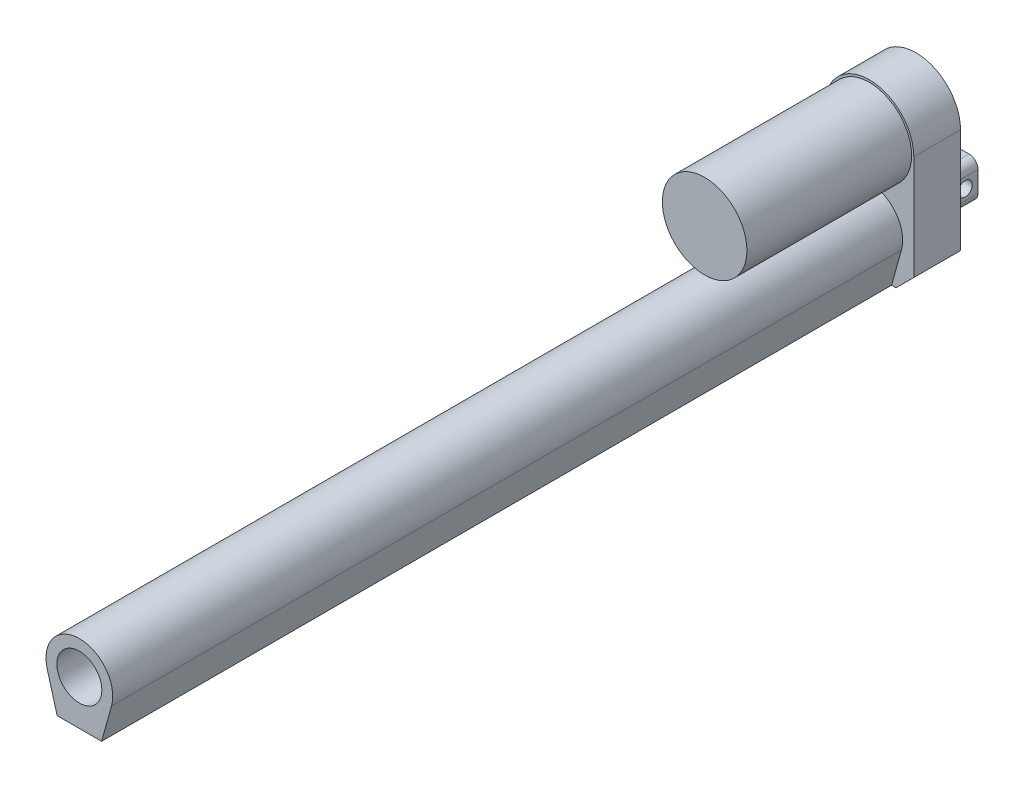
SolidWorks part; units mm, degrees
material "1060 Alloy"
ref_plane "Front Plane" through (0, 0, 0) normal (0, 0, 1) x (1, 0, 0)
ref_plane "Top Plane" through (0, 0, 0) normal (0, 1, 0) x (1, 0, 0)
ref_plane "Right Plane" through (0, 0, 0) normal (1, 0, 0) x (0, 0, -1)
sketch "Sketch1" plane through (0, 0, 0) normal (0, 0, 1) x (1, 0, 0)
  line L0 (-12, -37.5) -> (12, -37.5)
  line L1 (20, -37.5) -> (-20, -37.5) construction
  line L2 (20, -37.5) -> (20, 37.5) construction
  line L3 (20, 37.5) -> (-20, 37.5) construction
  line L4 (-20, -37.5) -> (-20, 37.5) construction
  line L5 (20, -37.5) -> (-20, 37.5) construction
  line L6 (20, 37.5) -> (-20, -37.5) construction
  line L7 (12, -37.5) -> (20, -29.5)
  line L8 (20, -29.5) -> (20, 17.5)
  line L9 (0, -55) -> (0, 55) construction
  line L10 (-12, -37.5) -> (-20, -29.5)
  line L11 (-20, -29.5) -> (-20, 17.5)
  arc A0 (20, 17.5) -> (-20, 17.5) centre (0, 17.5) ccw
  point P0 (0, 0)
  point P15 (0, -37.5)
  dimension "D3" = 20
  dimension "D1" = 40
  dimension "D2" = 75
  dimension "D4" = 12
  dimension "D5" = 45
extrude "Boss-Extrude1" add sketch "Sketch1" along normal blind 21
sketch "Sketch2" plane through (0, 0, 21) normal (0, 0, 1) x (1, 0, 0)
  circle A0 centre (0, 17.5) radius 19
  dimension "D1" = 38
extrude "Boss-Extrude2" add sketch "Sketch2" along normal blind 74
sketch "Sketch3" plane through (0, 0, 21) normal (0, 0, 1) x (1, 0, 0)
  line L0 (14.4499, -21.5251) -> (10, -37.5)
  line L1 (-12, -37.5) -> (12, -37.5) construction
  line L2 (0, -49.0716) -> (0, 47.8517) construction
  line L3 (-14.4499, -21.5251) -> (-10, -37.5)
  line L4 (-10, -37.5) -> (10, -37.5)
  arc A0 (14.4499, -21.5251) -> (-14.4499, -21.5251) centre (0, -17.5) ccw
  circle A1 centre (0, 17.5) radius 19 construction
  dimension "D1" = 30
  dimension "D2" = 1
  dimension "D3" = 20
extrude "Boss-Extrude3" add sketch "Sketch3" along normal blind 355
sketch "Sketch4" plane through (0, 0, 0) normal (0, 0, -1) x (-1, 0, 0)
  line L0 (0, 39.9784) -> (0, -62.5851) construction
  line L1 (-8.65, -26.5) -> (8.65, -26.5)
  line L2 (-8.65, -26.5) -> (-8.65, -9.2)
  line L3 (-8.65, -9.2) -> (8.65, -9.2)
  line L4 (8.65, -26.5) -> (8.65, -9.2)
  line L5 (-8.65, -26.5) -> (8.65, -9.2) construction
  line L6 (-8.65, -9.2) -> (8.65, -26.5) construction
  line L7 (12, -37.5) -> (-12, -37.5) construction
  point P0 (0, -17.85)
  dimension "D1" = 17.3
  dimension "D2" = 11
extrude "Boss-Extrude4" add sketch "Sketch4" along normal blind 19.2
sketch "Sketch5" plane through (0, 0, 376) normal (0, 0, 1) x (1, 0, 0)
  circle A0 centre (0, -17.5) radius 10.1
  dimension "D1" = 20.2
fillet "Fillet1" radius 4 4 edges at (-8.65, -9.2, -9.6) (8.65, -9.2, -9.6) (8.65, -26.5, -9.6) (-8.65, -26.5, -9.6)
extrude "Cut-Extrude1" cut sketch "Sketch5" against normal blind 300
sketch "Sketch6" plane through (0, 0, 0) normal (1, 0, 0) x (0, 0, -1)
  line L0 (19.2, -13.2) -> (19.2, -22.5) construction
  line L1 (19.2, -17.85) -> (0, -17.85) construction
  line L2 (0, -13.2) -> (0, -22.5) construction
  circle A0 centre (13.45, -17.85) radius 3.175
  dimension "D1" = 6.35
  dimension "D2" = 5.75
extrude "Cut-Extrude2" cut sketch "Sketch6" against normal through all both and the other way through all
